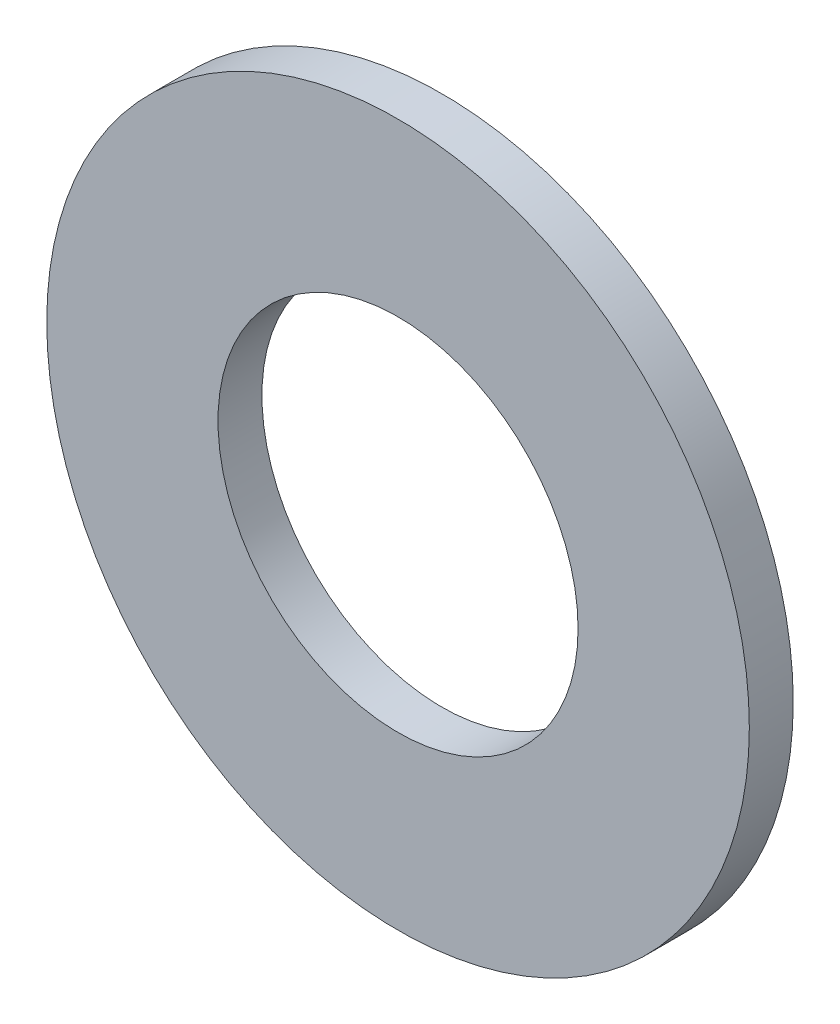
SolidWorks part; units mm, degrees
material "Plain Carbon Steel"
ref_plane "Front Plane" through (0, 0, 0) normal (0, 0, 1) x (1, 0, 0)
ref_plane "Top Plane" through (0, 0, 0) normal (0, 1, 0) x (1, 0, 0)
ref_plane "Right Plane" through (0, 0, 0) normal (1, 0, 0) x (0, 0, -1)
sketch "Sketch1" plane through (0, 0, 0) normal (0, 1, 0) x (1, 0, 0)
  line L0 (0, -20.3648) -> (0, 13.0529) construction
  line L1 (-8, 0.5) -> (-8, -0.5)
  line L2 (-8, -0.5) -> (0, -0.5)
  line L3 (0, -0.5) -> (0, 0.5)
  line L4 (0, 0.5) -> (-8, 0.5)
  line L5 (9.6434, 0) -> (-9.0324, 0) construction
  dimension "D1" = 16
  dimension "D2" = 1
revolve "Revolve1" add sketch "Sketch1" angle 360 about L0
hole_wizard "Ø8.2 (8.2) Diameter Hole1" positions "Sketch3" profile "Sketch2" hole size "Ø8.2" standard "DIN" end condition through all
sketch "Sketch3" plane through (0, 0, 0.5) normal (0, 0, 1) x (1, 0, 0)
  point P0 (0, 0)
sketch "Sketch2" plane through (0, 0, 0.5) normal (1, 0, 0) x (0, -1, 0)
  line L0 (0, 0) -> (0, 1)
  line L1 (0, 1) -> (4.1, 1)
  line L2 (4.1, 1) -> (4.1, 0)
  line L5 (4.1, 0) -> (0, 0)
  line L11 (0, -6.35) -> (0, 107.95) construction
  dimension "Thru Hole Dia." = 8.2
  dimension "Thru Hole Depth" = 1
